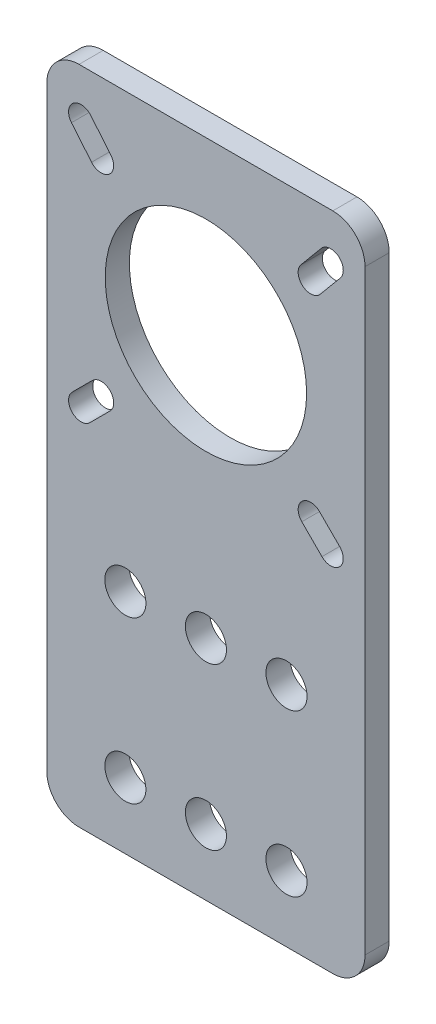
SolidWorks part; units mm, degrees
ref_plane "Piano frontale" through (0, 0, 0) normal (0, 0, 1) x (1, 0, 0)
ref_plane "Piano superiore" through (0, 0, 0) normal (0, 1, 0) x (1, 0, 0)
ref_plane "Piano destro" through (0, 0, 0) normal (1, 0, 0) x (0, 0, -1)
sketch "Schizzo1" plane through (0, 0, 0) normal (0, 0, 1) x (1, 0, 0)
  line L0 (-15.5, 35.25) -> (-13, 32.25) construction
  line L1 (-15.75, -41) -> (15.75, -41)
  line L2 (-19.75, -37) -> (-19.75, 37)
  line L3 (-15.75, 41) -> (15.75, 41)
  line L4 (19.75, -37) -> (19.75, 37)
  line L5 (-19.75, -41) -> (19.75, 41) construction
  line L6 (-19.75, 41) -> (19.75, -41) construction
  line L7 (-14.3093, 36.2423) -> (-11.8093, 33.2423)
  line L8 (-16.6907, 34.2577) -> (-14.1907, 31.2577)
  line L9 (0, 41) -> (0, -41) construction
  line L10 (15.5, 35.25) -> (13, 32.25) construction
  line L11 (14.3093, 36.2423) -> (11.8093, 33.2423)
  line L12 (16.6907, 34.2577) -> (14.1907, 31.2577)
  line L13 (-13, 6.75) -> (-15.5, 4.25) construction
  line L14 (-11.904, 5.654) -> (-14.404, 3.154)
  line L15 (-14.096, 7.846) -> (-16.596, 5.346)
  line L16 (13, 6.75) -> (15.5, 4.25) construction
  line L17 (11.904, 5.654) -> (14.404, 3.154)
  line L18 (14.096, 7.846) -> (16.596, 5.346)
  line L19 (-19.75, -12.8) -> (19.75, -12.8) construction
  line L20 (-19.75, -22.8) -> (19.75, -22.8) construction
  circle A0 centre (0, 19.75) radius 12.5
  arc A1 (-15.75, -41) -> (-19.75, -37) centre (-15.75, -37) cw
  arc A2 (15.75, -41) -> (19.75, -37) centre (15.75, -37) ccw
  arc A3 (15.75, 41) -> (19.75, 37) centre (15.75, 37) cw
  arc A4 (-19.75, 37) -> (-15.75, 41) centre (-15.75, 37) cw
  arc A5 (-14.3093, 36.2423) -> (-16.6907, 34.2577) centre (-15.5, 35.25) ccw
  arc A6 (-14.1907, 31.2577) -> (-11.8093, 33.2423) centre (-13, 32.25) ccw
  arc A7 (14.3093, 36.2423) -> (16.6907, 34.2577) centre (15.5, 35.25) cw
  arc A8 (14.1907, 31.2577) -> (11.8093, 33.2423) centre (13, 32.25) cw
  arc A9 (-11.904, 5.654) -> (-14.096, 7.846) centre (-13, 6.75) ccw
  arc A10 (-16.596, 5.346) -> (-14.404, 3.154) centre (-15.5, 4.25) ccw
  arc A11 (11.904, 5.654) -> (14.096, 7.846) centre (13, 6.75) cw
  arc A12 (16.596, 5.346) -> (14.404, 3.154) centre (15.5, 4.25) cw
  circle A13 centre (-10, -12.8) radius 2.55
  circle A14 centre (0, -12.8) radius 2.55
  circle A15 centre (10, -12.8) radius 2.55
  circle A16 centre (10, -32.8) radius 2.55
  circle A17 centre (0, -32.8) radius 2.55
  circle A18 centre (-10, -32.8) radius 2.55
  point P0 (0, 0)
  point P22 (-14.25, 33.75)
  point P31 (14.25, 33.75)
  point P38 (-14.25, 5.5)
  point P47 (14.25, 5.5)
  dimension "D5" = 4
  dimension "D10" = 1.55
  dimension "D11" = 25
  dimension "D12" = 1.55
  dimension "D15" = 5.1
  dimension "D1" = 39.5
  dimension "D2" = 82
  dimension "D3" = 21.25
  dimension "D4" = 19.75
  dimension "D6" = 4.25
  dimension "D7" = 5.75
  dimension "D8" = 8.75
  dimension "D9" = 6.75
  dimension "D13" = 34.25
  dimension "D14" = 36.75
  dimension "D16" = 53.8
  dimension "D17" = 9.75
  dimension "D18" = 29.75
  dimension "D19" = 63.8
extrude "Estrusione-Estrusione1" add sketch "Schizzo1" along normal blind 3
